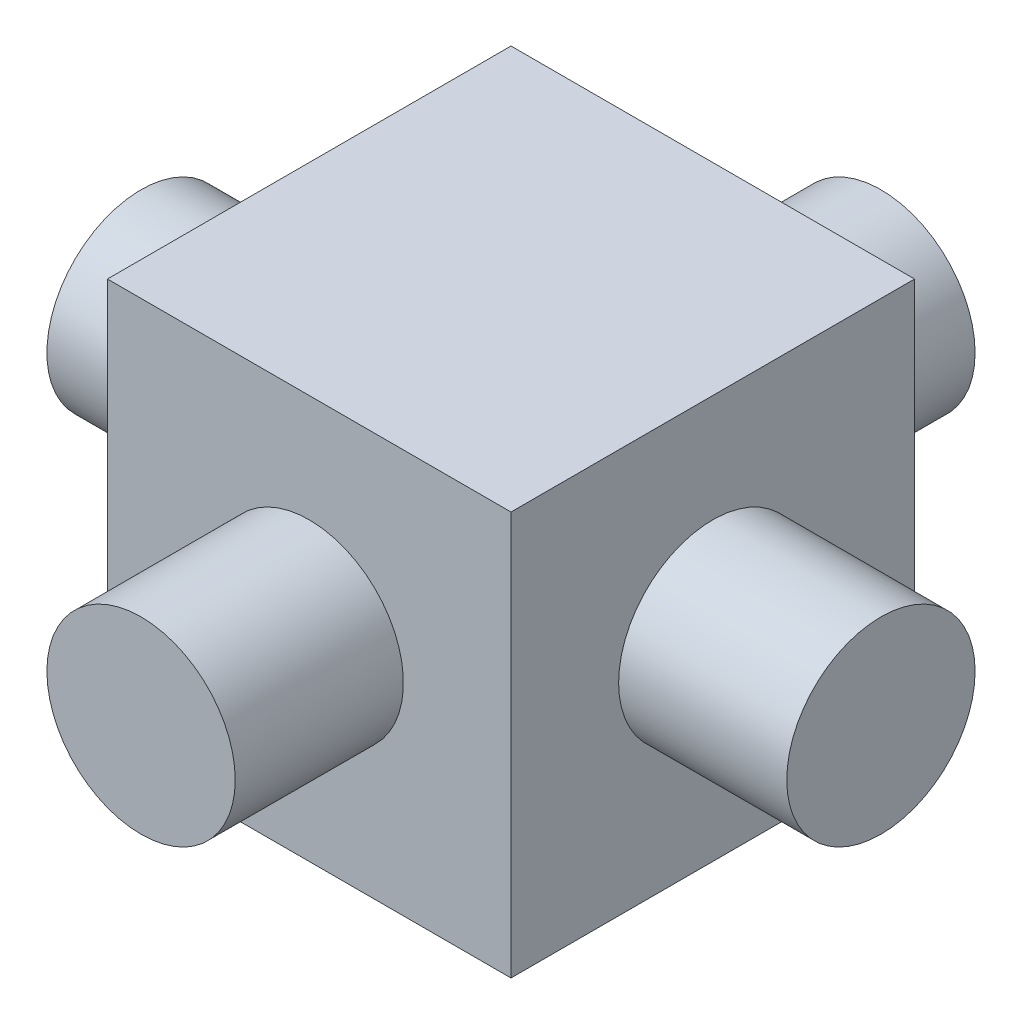
SolidWorks part; units mm, degrees
ref_plane "前视基准面" through (0, 0, 0) normal (0, 0, 1) x (1, 0, 0)
ref_plane "上视基准面" through (0, 0, 0) normal (0, 1, 0) x (1, 0, 0)
ref_plane "右视基准面" through (0, 0, 0) normal (1, 0, 0) x (0, 0, -1)
sketch "草图1" plane through (0, 0, 0) normal (0, 1, 0) x (1, 0, 0)
  line L1 (-3, 3) -> (3, 3)
  line L2 (-3, 3) -> (-3, -3)
  line L3 (-3, -3) -> (3, -3)
  line L4 (3, 3) -> (3, -3)
  line L5 (-3, 3) -> (3, -3) construction
  line L6 (-3, -3) -> (3, 3) construction
  point P0 (0, 0)
  dimension "D1" = 6
  dimension "D2" = 6
extrude "凸台-拉伸1" add sketch "草图1" along normal blind 6
sketch "草图2" plane through (0, 0, 0) normal (0, 0, 1) x (1, 0, 0)
  line L0 (-3, 6) -> (3, 6) construction
  line L1 (3, 6) -> (3, 0) construction
  circle A0 centre (0, 3) radius 1.4
  point P4 (0, 6)
  point P8 (3, 3)
  dimension "D1" = 2.8
extrude "凸台-拉伸2" add sketch "草图2" along normal mid plane 11
sketch "草图3" plane through (0, 0, 0) normal (1, 0, 0) x (0, 0, -1)
  line L0 (-3, 6) -> (3, 6) construction
  line L1 (3, 6) -> (3, 0) construction
  circle A0 centre (0, 3) radius 1.4
  point P4 (0, 6)
  point P7 (3, 3)
  dimension "D1" = 2.8
extrude "凸台-拉伸3" add sketch "草图3" along normal mid plane 11
ref_plane "基准面1" through (0, 3, 0) normal (0, 1, 0) x (1, 0, 0)
sketch "草图5" plane through (0, 3, 0) normal (0, 1, 0) x (1, 0, 0)
  circle A0 centre (0, 0) radius 1.5
  dimension "D1" = 3
